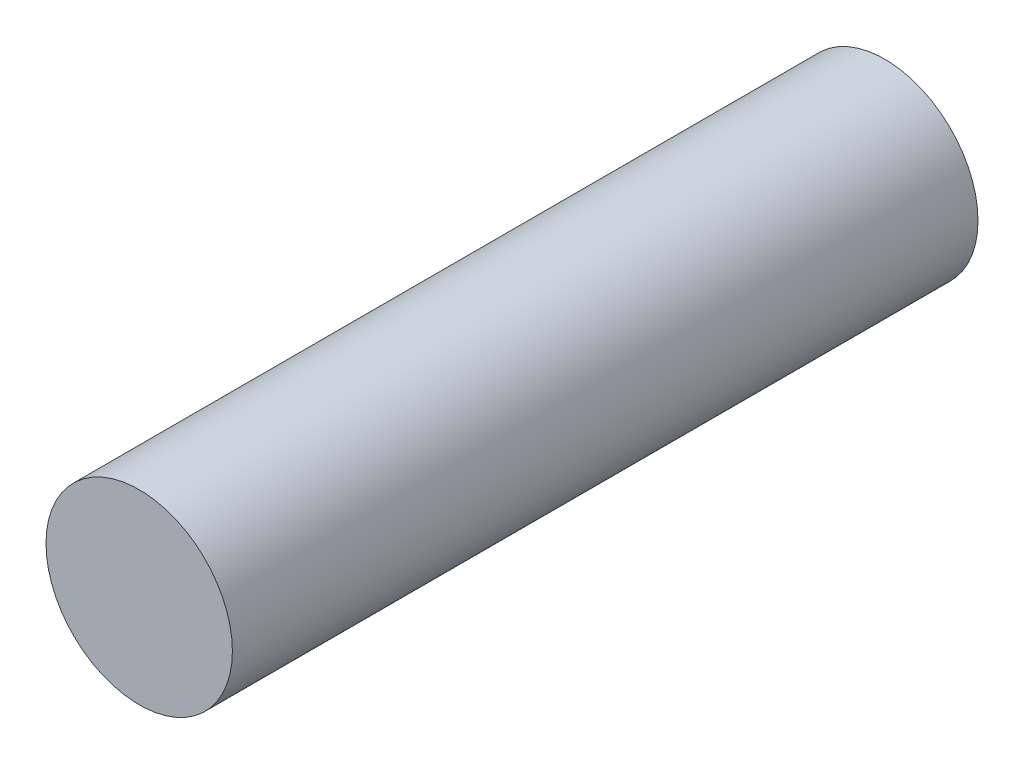
SolidWorks part; units mm, degrees
material "AISI 4130 Steel, normalized at 870C"
ref_plane "Front Plane" through (0, 0, 0) normal (0, 0, 1) x (1, 0, 0)
ref_plane "Top Plane" through (0, 0, 0) normal (0, 1, 0) x (1, 0, 0)
ref_plane "Right Plane" through (0, 0, 0) normal (1, 0, 0) x (0, 0, -1)
sketch "Sketch1" plane through (0, 0, 0) normal (0, 0, 1) x (1, 0, 0)
  circle A0 centre (0, 0) radius 3.9688
  dimension "D1" = 7.9375
extrude "Boss-Extrude1" add sketch "Sketch1" along normal mid plane 31.75
